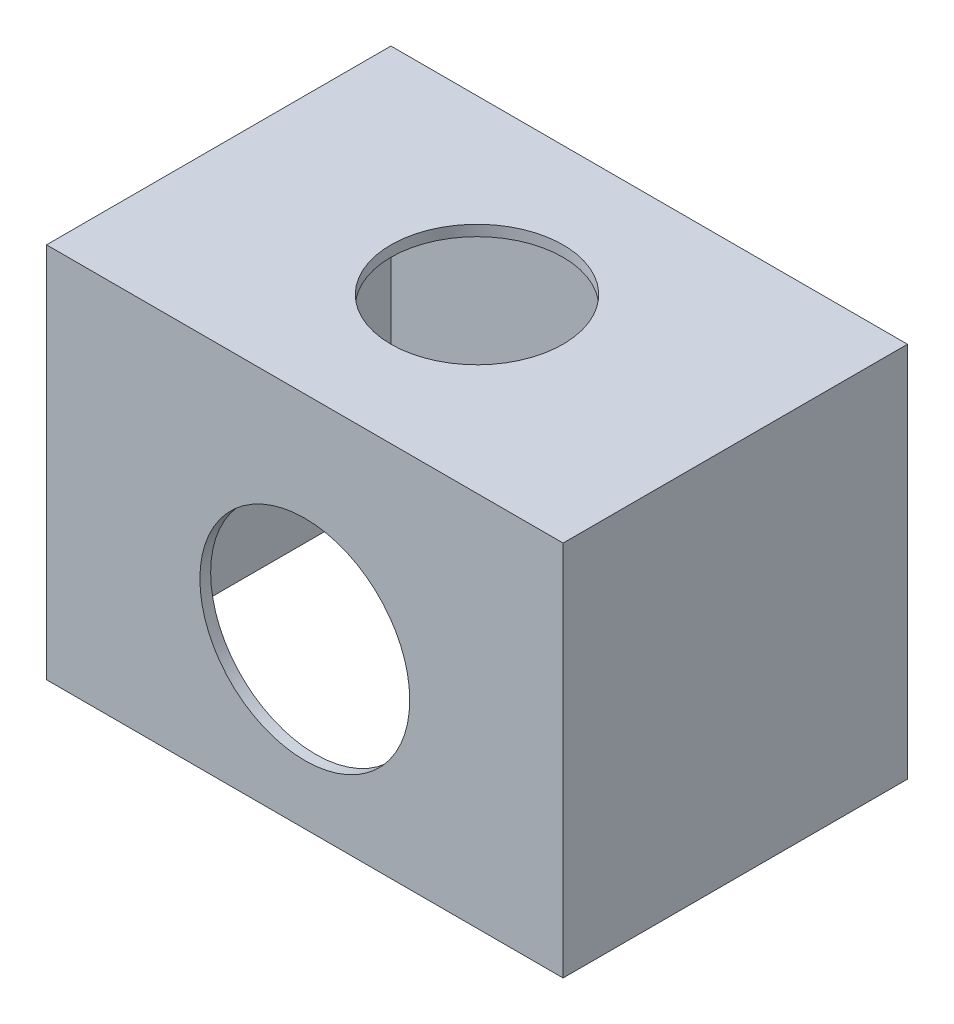
SolidWorks part; units mm, degrees
ref_plane "Alzado" through (0, 0, 0) normal (0, 0, 1) x (1, 0, 0)
ref_plane "Planta" through (0, 0, 0) normal (0, 1, 0) x (1, 0, 0)
ref_plane "Vista lateral" through (0, 0, 0) normal (1, 0, 0) x (0, 0, -1)
sketch "Croquis1" plane through (0, 0, 0) normal (0, 1, 0) x (1, 0, 0)
  line L1 (-48, -32) -> (48, -32)
  line L2 (-48, -32) -> (-48, 32)
  line L3 (-48, 32) -> (48, 32)
  line L4 (48, -32) -> (48, 32)
  line L5 (-48, -32) -> (48, 32) construction
  line L6 (-48, 32) -> (48, -32) construction
  point P0 (0, 0)
  dimension "D1" = 96
  dimension "D2" = 64
extrude "Saliente-Extruir1" add sketch "Croquis1" along normal blind 70
shell "Vaciado1" thickness 2
sketch "Croquis2" plane through (0, 70, 0) normal (0, 1, 0) x (1, 0, 0)
  circle A0 centre (0, 0) radius 16
  dimension "D1" = 32
extrude "Cortar-Extruir1" cut sketch "Croquis2" against normal blind 5
sketch "Croquis3" plane through (0, 0, 32) normal (0, 0, 1) x (1, 0, 0)
  line L0 (0, 0) -> (0, 30.5) construction
  line L1 (-48, 0) -> (48, 0) construction
  circle A1 centre (0, 30.5) radius 19.5
  dimension "D1" = 39
  dimension "D2" = 30.5
extrude "Cortar-Extruir2" cut sketch "Croquis3" against normal blind 5
